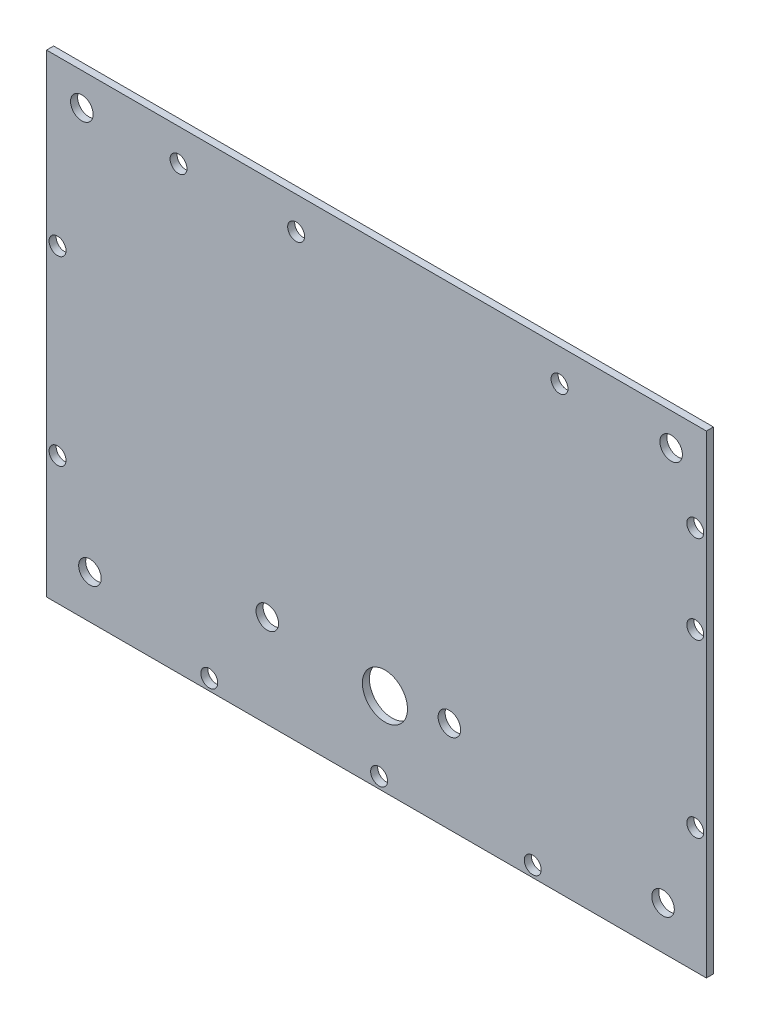
SolidWorks part; units mm, degrees
ref_plane "Front Plane" through (0, 0, 0) normal (0, 0, 1) x (1, 0, 0)
ref_plane "Top Plane" through (0, 0, 0) normal (0, 1, 0) x (1, 0, 0)
ref_plane "Right Plane" through (0, 0, 0) normal (1, 0, 0) x (0, 0, -1)
sketch "Sketch1" plane through (0, 0, 0) normal (0, 0, 1) x (1, 0, 0)
  line L1 (-74.295, -53.34) -> (74.295, -53.34)
  line L2 (-74.295, -53.34) -> (-74.295, 53.34)
  line L3 (-74.295, 53.34) -> (74.295, 53.34)
  line L4 (74.295, -53.34) -> (74.295, 53.34)
  line L5 (-74.295, -53.34) -> (74.295, 53.34) construction
  line L6 (-74.295, 53.34) -> (74.295, -53.34) construction
  point P0 (0, 0)
  dimension "D1" = 148.59
  dimension "D2" = 106.68
extrude "Boss-Extrude1" add sketch "Sketch1" along normal blind 1.5875
sketch "Sketch2" plane through (0, 0, 1.5875) normal (0, 0, 1) x (1, 0, 0)
  line L0 (0, -53.34) -> (0, 53.34) construction
  line L1 (-74.295, -53.34) -> (74.295, -53.34) construction
  line L2 (-74.295, -53.34) -> (-74.295, 53.34) construction
  line L4 (74.295, -53.34) -> (74.295, 53.34) construction
  line L5 (-74.295, -53.34) -> (74.295, 53.34) construction
  line L6 (-74.295, 53.34) -> (74.295, -53.34) construction
  line L7 (-74.295, 0) -> (74.295, 0) construction
  line L8 (-74.295, 50.8) -> (-58.42, 50.8) construction
  line L9 (-66.3575, 50.8) -> (-66.3575, -53.34) construction
  line L10 (74.295, 53.34) -> (-74.295, 53.34) construction
  circle A0 centre (-64.5325, -43.5775) radius 4.7625 construction
  circle A1 centre (-64.5325, -43.5775) radius 9.7625 construction
  circle A2 centre (-64.5325, -43.5775) radius 2.54
  circle A3 centre (64.5325, -43.5775) radius 2.54
  circle A6 centre (-66.3575, 46.0375) radius 4.7625 construction
  circle A7 centre (-66.3575, 46.0375) radius 2.54
  circle A8 centre (66.3575, 46.0375) radius 2.54
  point P0 (0, 0)
  dimension "D1" = 9.525
  dimension "D3" = 5.08
  dimension "D5" = 9.525
  dimension "D4" = 2.54
  dimension "D6" = 15.875
  dimension "D2" = 5
extrude "Cut-Extrude1" cut sketch "Sketch2" against normal through all
sketch "Sketch3" plane through (0, 0, 1.5875) normal (0, 0, 1) x (1, 0, 0)
  line L0 (-74.295, -53.34) -> (74.295, -53.34) construction
  line L1 (74.295, -53.34) -> (74.295, 53.34) construction
  circle A0 centre (1.905, -34.544) radius 5.08
  dimension "D1" = 10.16
  dimension "D2" = 18.796
  dimension "D3" = 72.39
extrude "Cut-Extrude2" cut sketch "Sketch3" against normal up to next
sketch "Sketch4" plane through (0, 0, 1.5875) normal (0, 0, 1) x (1, 0, 0)
  circle A1 centre (-44.5786, 46.0169) radius 1.905
  circle A2 centre (-18.0963, 46.0169) radius 1.905
  circle A3 centre (41.2226, 46.0169) radius 1.905
  circle A4 centre (71.795, 33.1997) radius 1.905
  circle A5 centre (71.795, 13.3752) radius 1.905
  circle A6 centre (71.795, -25.2459) radius 1.905
  circle A7 centre (35.1974, -50.84) radius 1.905
  circle A8 centre (0.5923, -50.84) radius 1.905
  circle A9 centre (-37.6555, -50.84) radius 1.905
  circle A10 centre (-71.8238, -24.5175) radius 1.905
  circle A11 centre (-71.8238, 16.3857) radius 1.905
  point P34 (0, 0)
  dimension "D1" = 3.81
extrude "Cut-Extrude3" cut sketch "Sketch4" against normal up to next
sketch "Sketch5" plane through (0, 0, 1.5875) normal (0, 0, 1) x (1, 0, 0)
  circle A0 centre (-24.5848, -32.4093) radius 2.54
  circle A1 centre (16.4151, -32.6176) radius 2.54
  dimension "D1" = 5.08
extrude "Cut-Extrude4" cut sketch "Sketch5" against normal up to next
